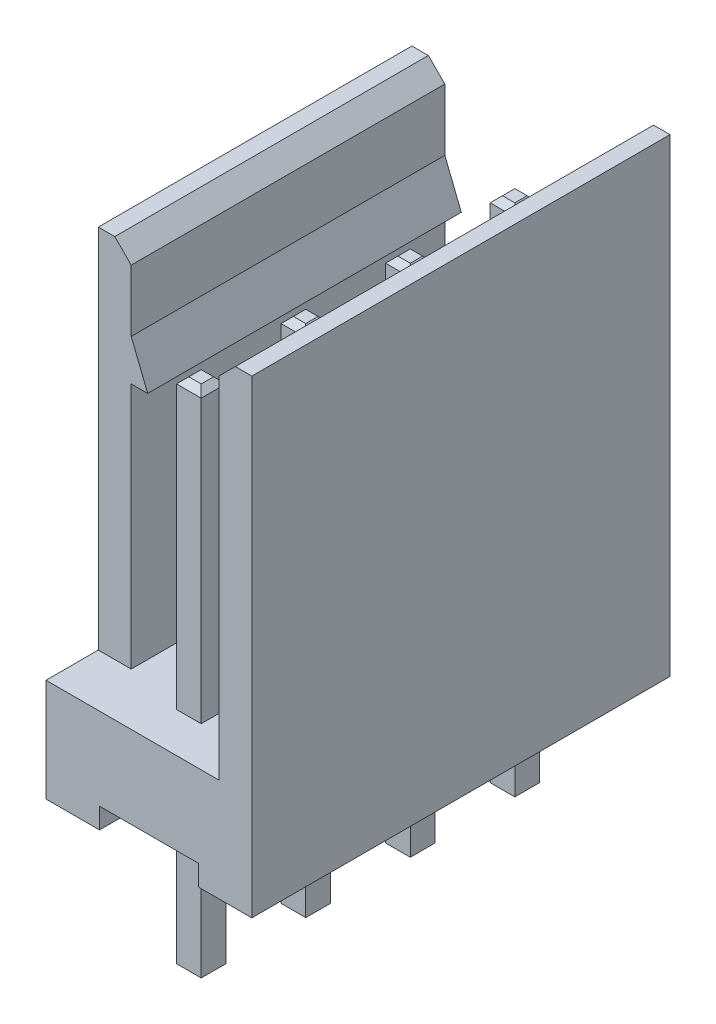
SolidWorks part; units mm, degrees
ref_plane "Plan de face" through (0, 0, 0) normal (0, 0, 1) x (1, 0, 0)
ref_plane "Plan de dessus" through (0, 0, 0) normal (0, 1, 0) x (1, 0, 0)
ref_plane "Plan de droite" through (0, 0, 0) normal (1, 0, 0) x (0, 0, -1)
sketch "Esquisse1" plane through (0, 0, 0) normal (0, 0, 1) x (1, 0, 0)
  line L0 (0, 11.4) -> (0, 0)
  line L1 (0, 0) -> (5, 0)
  line L2 (5, 0) -> (5, 11.4)
  line L3 (5, 11.4) -> (4.2, 11.4)
  line L4 (4.2, 11.4) -> (4.2, 2.5)
  line L5 (4.2, 2.5) -> (0.8, 2.5)
  line L6 (0.8, 2.5) -> (0.8, 11.4)
  line L10 (0.8, 11.4) -> (0, 11.4)
  dimension "D1" = 2.5
  dimension "D2" = 5
  dimension "D3" = 11.4
  dimension "D4" = 0.8
  dimension "D5" = 0.8
extrude "Boss.-Extru.1" add sketch "Esquisse1" along normal blind 10.16
sketch "Esquisse3" plane through (0, 11.4, 0) normal (0, 1, 0) x (1, 0, 0)
  line L0 (0.8, -10.16) -> (0.8, 0) construction
  line L1 (0, 0) -> (0.8, 0)
  line L2 (0, 0) -> (0, -1.27)
  line L3 (0, -1.27) -> (0.8, -1.27)
  line L4 (0.8, 0) -> (0.8, -1.27)
  line L6 (0, -10.16) -> (0.8, -10.16)
  line L7 (0, -10.16) -> (0, -8.89)
  line L8 (0, -8.89) -> (0.8, -8.89)
  line L9 (0.8, -10.16) -> (0.8, -8.89)
  dimension "D1" = 1.27
extrude "Enlèv. mat.-Extru.1" cut sketch "Esquisse3" against normal up to surface (8.9 mm away) up to face at (2.5, 2.5, 5.08)
sketch "Esquisse4" plane through (0, 0, 10.16) normal (0, 0, 1) x (1, 0, 0)
  line L0 (0, 0) -> (5, 0) construction
  line L1 (1.3, 0) -> (3.7, 0)
  line L2 (1.3, 0) -> (1.3, 0.5)
  line L3 (1.3, 0.5) -> (3.7, 0.5)
  line L4 (3.7, 0) -> (3.7, 0.5)
  line L5 (0, 2.5) -> (0, 0) construction
  line L6 (5, 0) -> (5, 11.4) construction
  point P8 (0, 1.25)
  dimension "D1" = 0.5
  dimension "D2" = 1.3
  dimension "D3" = 1.3
extrude "Enlèv. mat.-Extru.2" cut sketch "Esquisse4" against normal through all
sketch "Esquisse2" plane through (0, 0.5, 0) normal (0, -1, 0) x (1, 0, 0)
  line L0 (2.5, 8.89) -> (2.5, 10.16) construction
  line L1 (2.2, 8.59) -> (2.8, 8.59)
  line L2 (2.2, 8.59) -> (2.2, 9.19)
  line L3 (2.2, 9.19) -> (2.8, 9.19)
  line L4 (2.8, 8.59) -> (2.8, 9.19)
  line L5 (2.2, 8.59) -> (2.8, 9.19) construction
  line L6 (2.2, 9.19) -> (2.8, 8.59) construction
  line L7 (2.2, 0.97) -> (2.8, 0.97)
  line L8 (2.2, 0.97) -> (2.2, 1.57)
  line L9 (2.2, 1.57) -> (2.8, 1.57)
  line L10 (2.8, 0.97) -> (2.8, 1.57)
  line L11 (2.2, 0.97) -> (2.8, 1.57) construction
  line L12 (2.2, 1.57) -> (2.8, 0.97) construction
  line L13 (2.5, 8.89) -> (2.5, 6.35) construction
  line L14 (2.2, 6.65) -> (2.8, 6.65)
  line L15 (2.2, 6.65) -> (2.2, 6.05)
  line L16 (2.5, 1.27) -> (2.5, 0) construction
  line L17 (2.2, 6.05) -> (2.8, 6.05)
  line L18 (3.7, 10.16) -> (1.3, 10.16) construction
  line L19 (3.7, 0) -> (1.3, 0) construction
  line L20 (2.8, 6.65) -> (2.8, 6.05)
  line L21 (2.2, 6.65) -> (2.8, 6.05) construction
  line L22 (2.2, 6.05) -> (2.8, 6.65) construction
  line L29 (2.2, 4.11) -> (2.8, 4.11)
  line L30 (2.2, 4.11) -> (2.2, 3.51)
  line L31 (2.2, 3.51) -> (2.8, 3.51)
  line L32 (2.8, 4.11) -> (2.8, 3.51)
  line L33 (2.2, 4.11) -> (2.8, 3.51) construction
  line L34 (2.2, 3.51) -> (2.8, 4.11) construction
  line L35 (2.5, 6.35) -> (2.5, 3.81) construction
  line L37 (2.5, 3.81) -> (2.5, 1.27) construction
  point P0 (2.5, 8.89)
  point P5 (2.5, 1.27)
  point P12 (2.5, 3.8306)
  point P16 (2.5, 6.35)
  point P28 (2.5, 3.81)
  dimension "D1" = 0.6
  dimension "D2" = 2.54
extrude "Boss.-Extru.2" add sketch "Esquisse2" along normal blind 3.5 and the other way blind 9
sketch "Esquisse5" plane through (0, 0, 8.89) normal (0, 0, 1) x (1, 0, 0)
  line L0 (0.8, 9.5) -> (1.2, 8.5)
  line L1 (0.8, 2.5) -> (0.8, 11.4) construction
  line L2 (1.2, 8.5) -> (0.8, 8.5)
  line L3 (0.8, 8.5) -> (0.8, 9.5)
  line L4 (2.8, 9.5) -> (2.2, 9.5) construction
  dimension "D1" = 1
  dimension "D2" = 0.4
extrude "Boss.-Extru.3" add sketch "Esquisse5" against normal up to surface (7.62 mm away) up to face at (0.4, 6.95, 1.27)
chamfer "Chanfrein4" distance 0.15 angle 45 32 edges at (2.5, -3, 8.59) (2.2, -3, 8.89) (2.5, -3, 9.19) (2.8, -3, 8.89) (2.5, -3, 0.97) (2.2, -3, 1.27) (2.5, -3, 1.57) (2.8, -3, 1.27) (2.5, 9.5, 9.19) (2.2, 9.5, 8.89) (2.5, 9.5, 8.59) (2.8, 9.5, 8.89) (2.5, 9.5, 1.57) (2.2, 9.5, 1.27) (2.5, 9.5, 0.97) (2.8, 9.5, 1.27) (2.5, -3, 3.51) (2.2, -3, 3.81) (2.5, -3, 4.11) (2.8, -3, 3.81) (2.5, -3, 6.05) (2.2, -3, 6.35) (2.5, -3, 6.65) (2.8, -3, 6.35) (2.5, 9.5, 4.11) (2.2, 9.5, 3.81) (2.5, 9.5, 3.51) (2.8, 9.5, 3.81) (2.5, 9.5, 6.65) (2.2, 9.5, 6.35) (2.5, 9.5, 6.05) (2.8, 9.5, 6.35)
chamfer "Chanfrein5" distance 0.4 angle 45 2 edges at (4.2, 11.4, 5.08) (0.8, 11.4, 5.08)
